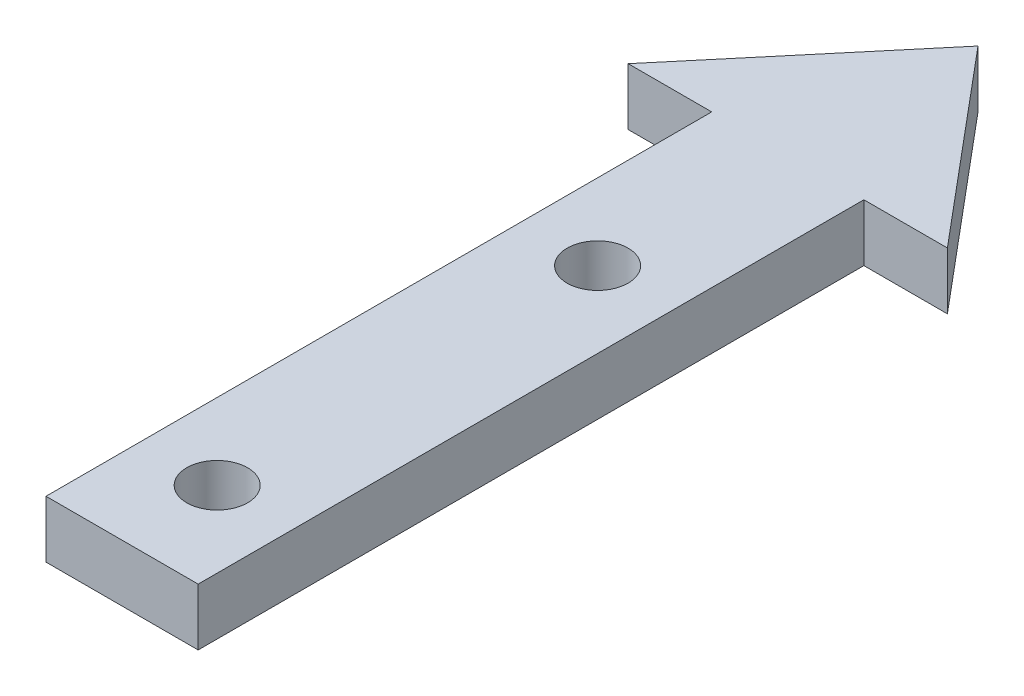
SolidWorks part; units mm, degrees
ref_plane "Front Plane" through (0, 0, 0) normal (0, 0, 1) x (1, 0, 0)
ref_plane "Top Plane" through (0, 0, 0) normal (0, 1, 0) x (1, 0, 0)
ref_plane "Right Plane" through (0, 0, 0) normal (1, 0, 0) x (0, 0, -1)
sketch "Sketch1" plane through (0, 0, 0) normal (0, 1, 0) x (1, 0, 0)
  line L0 (0, 0) -> (0, 60.3074) construction
  line L1 (0, 48.2697) -> (-8.391, 38.2697)
  line L2 (-4, 3.2697) -> (4, 3.2697)
  line L3 (-4, 3.2697) -> (-4, 38.2697)
  line L5 (4, 3.2697) -> (4, 38.2697)
  line L8 (-8.391, 38.2697) -> (8.391, 38.2697)
  line L9 (0, 48.2697) -> (8.391, 38.2697)
  circle A0 centre (0, 8.2697) radius 1.6
  circle A1 centre (0, 28.2697) radius 1.6
  point P3 (0, 23.4221)
  point P12 (0, 38.2697)
  dimension "D5" = 3.2
  dimension "D6" = 3.2
  dimension "D8" = 20
  dimension "D1" = 35
  dimension "D2" = 8
  dimension "D3" = 40
  dimension "D4" = 10
  dimension "D7" = 5
extrude "Boss-Extrude1" add sketch "Sketch1" along normal blind 3 contours L0 L8 L9 | L8 L0 L1 | L2 L0 A0 A1 L8 L3 | L0 L2 L5 L8 A1 A0
